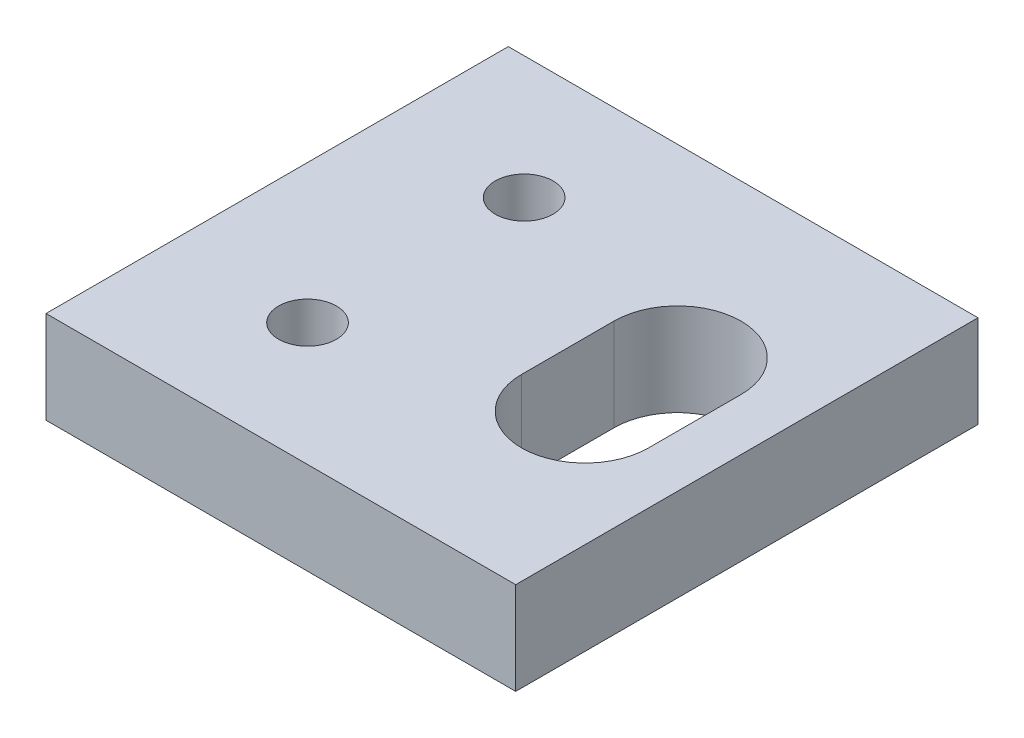
SolidWorks part; units mm, degrees
material "ABS"
ref_plane "Front Plane" through (0, 0, 0) normal (0, 0, 1) x (1, 0, 0)
ref_plane "Top Plane" through (0, 0, 0) normal (0, 1, 0) x (1, 0, 0)
ref_plane "Right Plane" through (0, 0, 0) normal (1, 0, 0) x (0, 0, -1)
ref_plane "Plane1" through (0, 4, 0) normal (0, 1, 0) x (1, 0, 0)
sketch "Sketch1" plane through (0, 4, 0) normal (0, 1, 0) x (1, 0, 0)
  line L0 (0, -10) -> (20.32, -10) construction
  line L2 (0, -20) -> (20.32, -20)
  line L3 (20.32, -20) -> (20.32, 0)
  line L4 (20.32, 0) -> (0, 0)
  line L5 (0, 0) -> (0, -20)
  line L6 (15.32, -12) -> (15.32, -8) construction
  line L7 (12.57, -12) -> (12.57, -8)
  line L8 (18.07, -12) -> (18.07, -8)
  circle A0 centre (6, -14.686) radius 1.25
  circle A3 centre (6, -5.314) radius 1.25
  arc A4 (12.57, -12) -> (18.07, -12) centre (15.32, -12) ccw
  arc A5 (18.07, -8) -> (12.57, -8) centre (15.32, -8) ccw
  point P16 (15.32, -10)
  dimension "D1" = 20.32
  dimension "D2" = 2.75
  dimension "D5" = 2.5
  dimension "D3" = 20
  dimension "D4" = 4
  dimension "D6" = 5
  dimension "D7" = 6
  dimension "D8" = 9.372
  dimension "D10" = 10
extrude "Boss-Extrude1" add sketch "Sketch1" against normal blind 4
